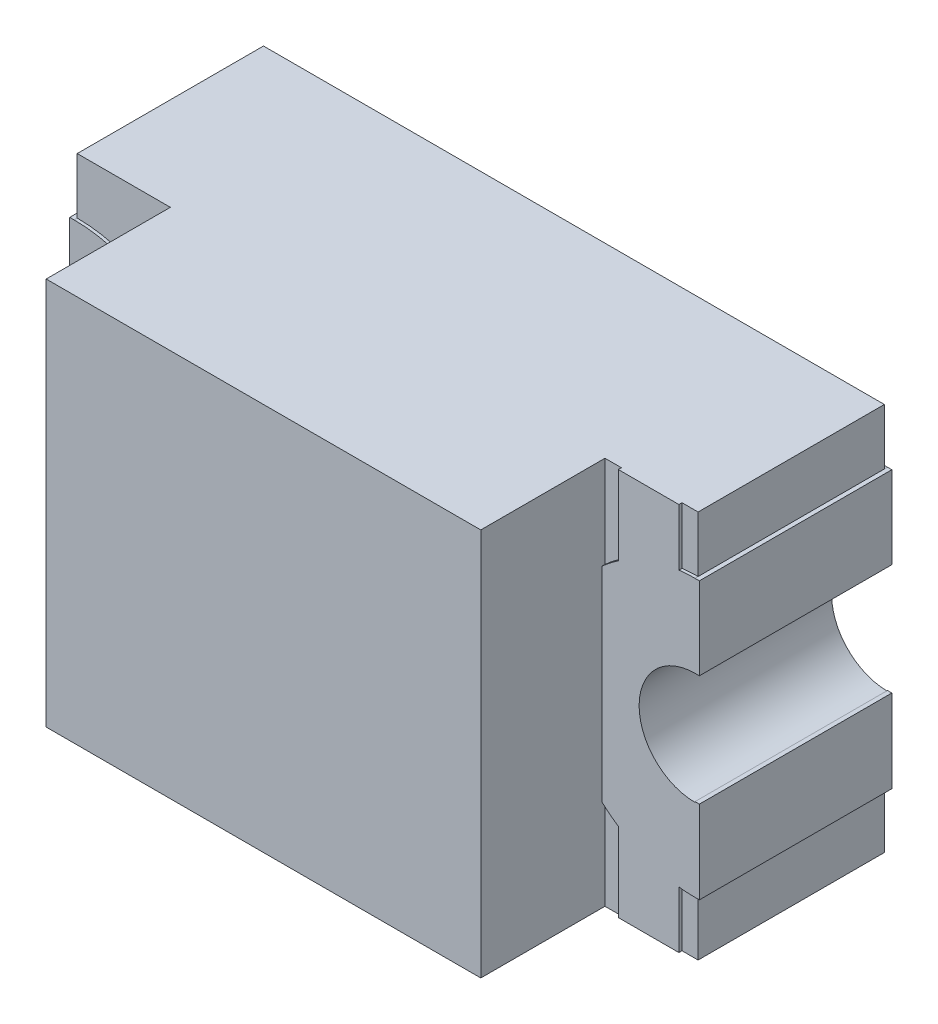
SolidWorks part; units mm, degrees
ref_plane "Front Plane" through (0, 0, 0) normal (0, 0, 1) x (1, 0, 0)
ref_plane "Top Plane" through (0, 0, 0) normal (0, 1, 0) x (1, 0, 0)
ref_plane "Right Plane" through (0, 0, 0) normal (1, 0, 0) x (0, 0, -1)
sketch "Sketch1" plane through (0, 0, 0) normal (0, 0, 1) x (1, 0, 0)
  line L1 (0, 0) -> (2, 0)
  line L2 (0, 0) -> (0, 1.25)
  line L3 (0, 1.25) -> (2, 1.25)
  line L4 (2, 0) -> (2, 1.25)
  dimension "D1" = 2
  dimension "D2" = 1.25
extrude "Boss-Extrude1" add sketch "Sketch1" along normal blind 0.6
sketch "Sketch2" plane through (0, 0, 0) normal (0, 0, 1) x (1, 0, 0)
  line L2 (2, 1.25) -> (0, 1.25) construction
  line L4 (0.3, 0) -> (1.7, 0)
  line L5 (0.3, 0) -> (0.3, 1.25)
  line L6 (0.3, 1.25) -> (1.7, 1.25)
  line L7 (1.7, 0) -> (1.7, 1.25)
  line L8 (0.3, 0) -> (1.7, 1.25) construction
  line L9 (0.3, 1.25) -> (1.7, 0) construction
  point P0 (0, 0)
  point P4 (1, 0.625)
extrude "Boss-Extrude2" add sketch "Sketch2" along normal blind 1
sketch "Sketch3" plane through (0, 0, 0) normal (0, 0, 1) x (1, 0, 0)
  line L0 (0, 1.25) -> (0, 0) construction
  line L1 (0, 1.07) -> (0, 0.18)
  circle A0 centre (0, 0.625) radius 0.445
extrude "Boss-Extrude3" add sketch "Sketch3" along normal blind 0.62 from offset 0.01 contours L1 A0 offset against normal yes
ref_plane "Plane1" through (1, 0, 0) normal (1, 0, 0) x (0, 0, -1)
mirror "Mirror1" about plane through (1, 0, 0) normal (1, 0, 0) of "Boss-Extrude3"
sketch "Sketch4" plane through (0, 0, 0) normal (0, 0, 1) x (1, 0, 0)
  line L0 (2, 1.25) -> (1.7, 1.25) construction
  line L1 (1.7528, 1.25) -> (1.9482, 1.25)
  line L2 (1.7528, 1.25) -> (1.7528, 0)
  line L3 (1.7528, 0) -> (1.9482, 0)
  line L4 (1.9482, 1.25) -> (1.9482, 0)
  line L5 (1.7, 0) -> (2, 0) construction
  point P8 (1.7816, -0.1453)
extrude "Boss-Extrude4" add sketch "Sketch4" along normal blind 0.61
sketch "Sketch7" plane through (0, 0, 0) normal (0, 0, 1) x (1, 0, 0)
  line L6 (1.9709, 1.16) -> (1.5574, 1.16)
  line L7 (1.9709, 1.16) -> (1.9709, 0.09)
  line L8 (1.9709, 0.09) -> (1.5574, 0.09)
  line L9 (1.5574, 1.16) -> (1.5574, 0.09)
  point P0 (0, 0)
extrude "Boss-Extrude5" add sketch "Sketch7" against normal blind 0.01
mirror "Mirror2" about plane through (1, 0, 0) normal (1, 0, 0) of "Boss-Extrude5"
sketch "Sketch8" plane through (0, 0, 0) normal (0, 0, 1) x (1, 0, 0)
  line L0 (0, 1.07) -> (0, 0.18) construction
  circle A0 centre (0, 0.625) radius 0.18
extrude "Cut-Extrude1" cut sketch "Sketch8" against normal through all both and the other way through all
mirror "Mirror3" about plane through (1, 0, 0) normal (1, 0, 0) of "Cut-Extrude1"
sketch "Sketch9" plane through (0, 0, 0) normal (0, 0, 1) x (1, 0, 0)
  line L1 (0, 0.805) -> (-0.0141, 0.805)
  line L2 (0, 0.805) -> (0, 1.07)
  line L3 (0, 1.07) -> (-0.0141, 1.07)
  line L4 (-0.0141, 0.805) -> (-0.0141, 1.07)
  line L5 (0, 0.18) -> (-0.0141, 0.18)
  line L6 (0, 0.18) -> (0, 0.4471)
  line L7 (0, 0.4471) -> (-0.0141, 0.4471)
  line L8 (-0.0141, 0.18) -> (-0.0141, 0.4471)
  point P10 (0, 0)
extrude "Boss-Extrude6" add sketch "Sketch9" along normal blind 0.62 from offset 0.01 offset against normal yes
mirror "Mirror4" about plane through (1, 0, 0) normal (1, 0, 0) of "Boss-Extrude6"
